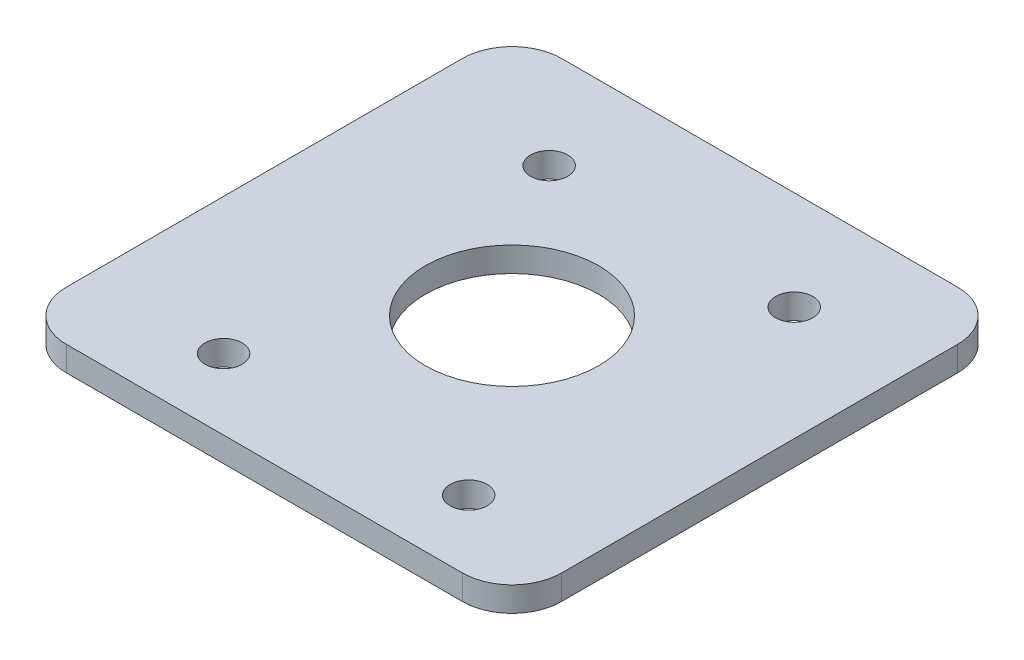
SolidWorks part; units mm, degrees
ref_plane "Front Plane" through (0, 0, 0) normal (0, 0, 1) x (1, 0, 0)
ref_plane "Top Plane" through (0, 0, 0) normal (0, 1, 0) x (1, 0, 0)
ref_plane "Right Plane" through (0, 0, 0) normal (1, 0, 0) x (0, 0, -1)
sketch "Sketch2" plane through (0, 0, 0) normal (0, 1, 0) x (1, 0, 0)
  line L0 (-9, 12) -> (-9, -14.3) construction
  line L1 (-20, 20) -> (20, 20)
  line L2 (-20, 20) -> (-20, -20)
  line L3 (-20, -20) -> (20, -20)
  line L4 (20, 20) -> (20, -20)
  line L5 (-20, 20) -> (20, -20) construction
  line L6 (-20, -20) -> (20, 20) construction
  line L7 (-9, 12) -> (10.8, 12) construction
  circle A0 centre (0, 0) radius 7
  circle A1 centre (-9, 12) radius 1.5
  circle A2 centre (-9, -14.3) radius 1.5
  circle A3 centre (10.8, -14.3) radius 1.5
  circle A4 centre (10.8, 12) radius 1.5
  point P0 (0, 0)
  point P16 (0, 0)
  point P17 (0, 0)
  dimension "D1" = 19.8
  dimension "D3" = 14
  dimension "D4" = 3
  dimension "D5" = 40
  dimension "D2" = 26.3
  dimension "D6" = 40
  dimension "D7" = 12
  dimension "D8" = 9
extrude "Boss-Extrude1" add sketch "Sketch2" along normal blind 2
fillet "Fillet1" radius 4 4 edges at (-20, 1, 20) (20, 1, 20) (20, 1, -20) (-20, 1, -20)
